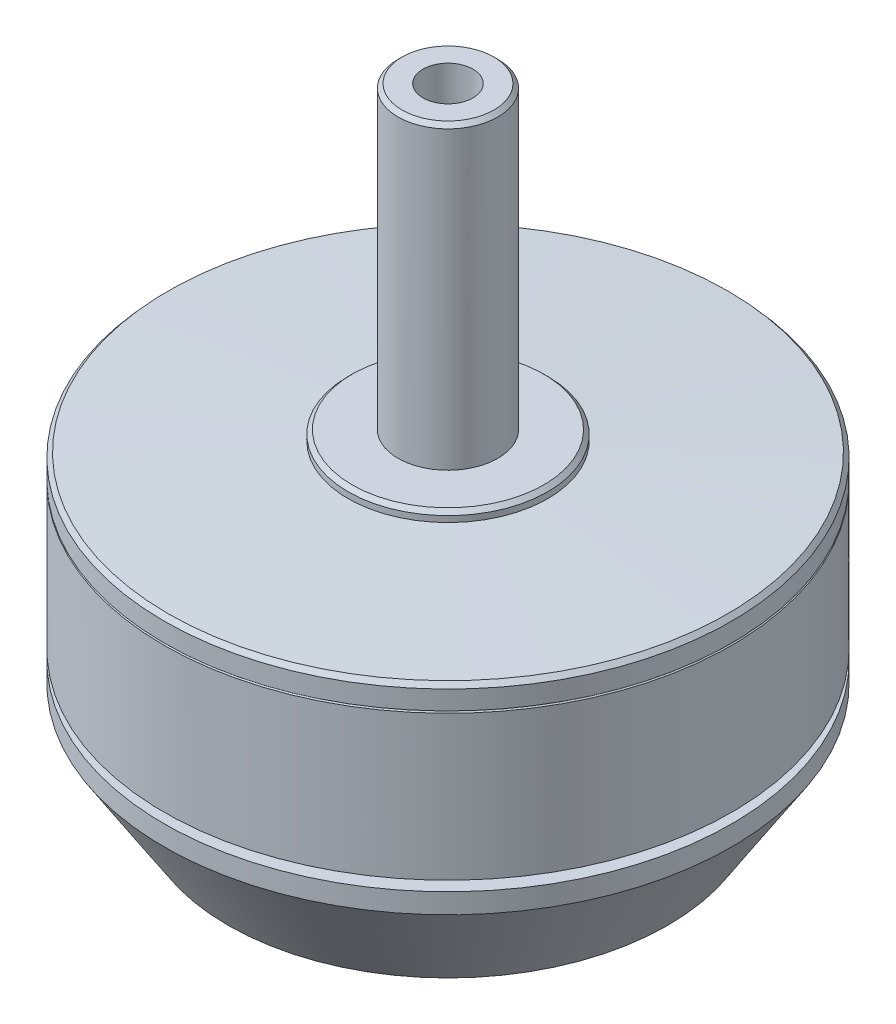
SolidWorks part; units mm, degrees
ref_plane "前视基准面" through (0, 0, 0) normal (0, 0, 1) x (1, 0, 0)
ref_plane "上视基准面" through (0, 0, 0) normal (0, 1, 0) x (1, 0, 0)
ref_plane "右视基准面" through (0, 0, 0) normal (1, 0, 0) x (0, 0, -1)
sketch "草图1" plane through (0, 0, 0) normal (0, 0, 1) x (1, 0, 0)
  line L0 (0, 0.7508) -> (0, 19.0598)
  line L1 (6, 0) -> (11, 0)
  line L2 (14.2, 5) -> (14.2, 6)
  line L3 (6, 0) -> (6, 0.7508)
  line L4 (14.2, 6.5) -> (11, 6.5)
  line L5 (14.2, 6.5) -> (14.2, 15)
  line L6 (5, 16) -> (2.5, 16)
  line L7 (14.2, 6) -> (11, 6)
  line L8 (11, 0) -> (14.2, 5)
  line L9 (0, 19.0598) -> (1.25, 19.0598)
  line L10 (11, 6.5) -> (11, 6)
  line L11 (14.2, 6) -> (0, 6) construction
  line L12 (14.2, 6.5) -> (0, 6.5) construction
  line L13 (5, 16) -> (5, 15.5)
  line L14 (6, 0.7508) -> (0, 0.7508)
  line L15 (5, 15.5) -> (14.2, 15)
  line L16 (1.25, 31) -> (2.5, 31)
  line L17 (2.5, 31) -> (2.5, 16)
  line L18 (1.25, 19.0598) -> (1.25, 31)
  dimension "D1" = 1.25
  dimension "D2" = 16
  dimension "D3" = 0.5
  dimension "D4" = 5
  dimension "D6" = 6
  dimension "D7" = 31
  dimension "D5" = 11.9402
  dimension "D8" = 2.5
revolve "旋转1" add sketch "草图1" angle 360 about L0
chamfer "倒角1" distance 0.2 angle 45 4 edges at (0, 15, -14.2) (0, 16, -5) (0, 31, -2.5) (0, 0, -6)
ref_axis "基准轴1" through (0, 32.55, 0) along (0, -1, 0)
sketch "草图4" plane through (0, 0, 0) normal (0, 0, 1) x (1, 0, 0)
  line L0 (-14.2, 14.7882) -> (14.2, 14.7882) construction
  circle A0 centre (14.1938, 13.7882) radius 0.05
  dimension "D1" = 0.1
  dimension "D2" = 1
revolve "切除-旋转4" cut sketch "草图4" angle 360 about axis through (0, 32.55, 0) along (0, -1, 0)
